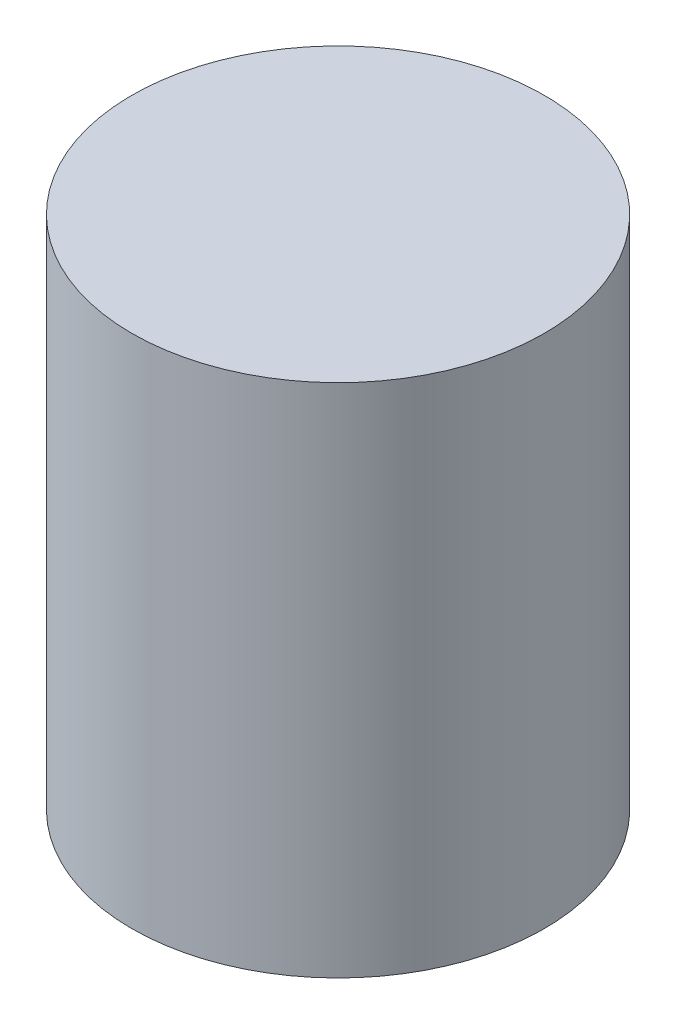
SolidWorks part; units mm, degrees
ref_plane "Front Plane" through (0, 0, 0) normal (0, 0, 1) x (1, 0, 0)
ref_plane "Top Plane" through (0, 0, 0) normal (0, 1, 0) x (1, 0, 0)
ref_plane "Right Plane" through (0, 0, 0) normal (1, 0, 0) x (0, 0, -1)
sketch "Sketch1" plane through (0, 0, 0) normal (0, 1, 0) x (1, 0, 0)
  circle A0 centre (0, 0) radius 20
  dimension "D1" = 40
extrude "Boss-Extrude1" add sketch "Sketch1" along normal blind 50
